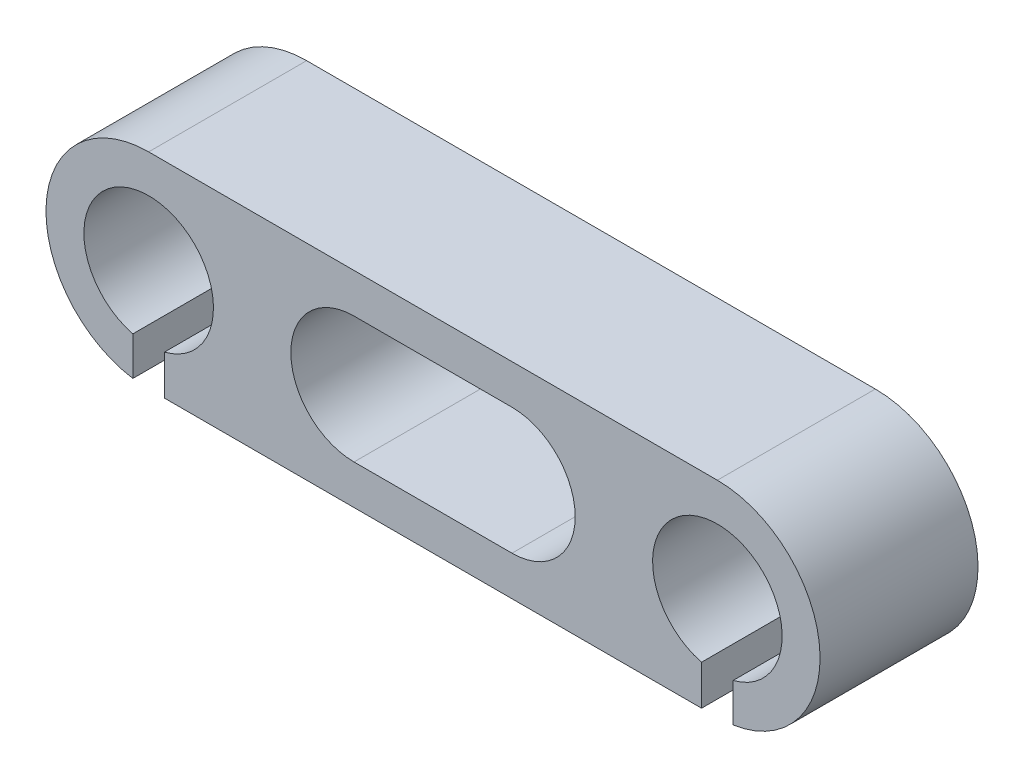
SolidWorks part; units mm, degrees
ref_plane "Front Plane" through (0, 0, 0) normal (0, 0, 1) x (1, 0, 0)
ref_plane "Top Plane" through (0, 0, 0) normal (0, 1, 0) x (1, 0, 0)
ref_plane "Right Plane" through (0, 0, 0) normal (1, 0, 0) x (0, 0, -1)
sketch "Sketch1" plane through (0, 0, 0) normal (0, 0, 1) x (1, 0, 0)
  line L0 (0, 3.25) -> (18, 3.25)
  line L1 (0, -3.25) -> (18, -3.25)
  line L2 (9, 3.25) -> (9, -3.25) construction
  line L3 (11.5, 0) -> (6.5, 0) construction
  line L4 (11.5, -2) -> (6.5, -2)
  line L5 (11.5, 2) -> (6.5, 2)
  circle A0 centre (0, 0) radius 2.05
  circle A1 centre (18, 0) radius 2.05
  arc A2 (0, 3.25) -> (0, -3.25) centre (0, 0) ccw
  arc A3 (18, -3.25) -> (18, 3.25) centre (18, 0) ccw
  arc A4 (11.5, -2) -> (11.5, 2) centre (11.5, 0) ccw
  arc A5 (6.5, 2) -> (6.5, -2) centre (6.5, 0) ccw
  point P15 (9, 0)
  dimension "D1" = 4.1
  dimension "D2" = 1.2
  dimension "D4" = 2
  dimension "D3" = 18
  dimension "D5" = 5
extrude "Boss-Extrude1" add sketch "Sketch1" along normal blind 5
sketch "Sketch2" plane through (0, -3.25, 0) normal (0, -1, 0) x (-1, 0, 0)
  line L0 (0, -5) -> (0, 0)
  line L1 (-18, -5) -> (-18, 0)
extrude "Cut-Extrude-Thin1" cut sketch "Sketch2" against normal blind 2 thin thin type mid plane wall 1
